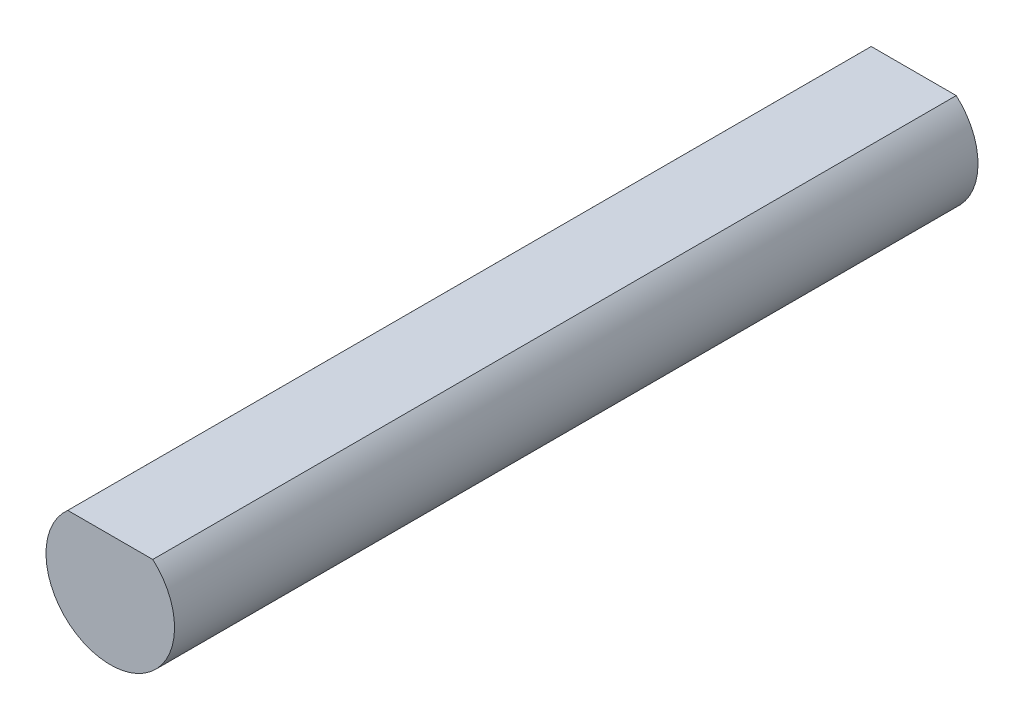
SolidWorks part; units mm, degrees
ref_plane "Front Plane" through (0, 0, 0) normal (0, 0, 1) x (1, 0, 0)
ref_plane "Top Plane" through (0, 0, 0) normal (0, 1, 0) x (1, 0, 0)
ref_plane "Right Plane" through (0, 0, 0) normal (1, 0, 0) x (0, 0, -1)
sketch "Sketch1" plane through (0, 0, 0) normal (0, 0, 1) x (1, 0, 0)
  line L0 (-1.3229, 1.5) -> (1.3229, 1.5)
  line L1 (0, 0.005) -> (0, -2) construction
  line L2 (0, 0) -> (2, 0) construction
  arc A0 (-1.3229, 1.5) -> (1.3229, 1.5) centre (0, 0) ccw
  point P5 (0, 1.5)
  point P9 (1, 0)
  dimension "D1" = 4
  dimension "D2" = 1.5
extrude "Boss-Extrude1" add sketch "Sketch1" along normal blind 25
equation "\"height\"= 25mm"
equation "\"D1@Boss-Extrude1\"=\"height\""
